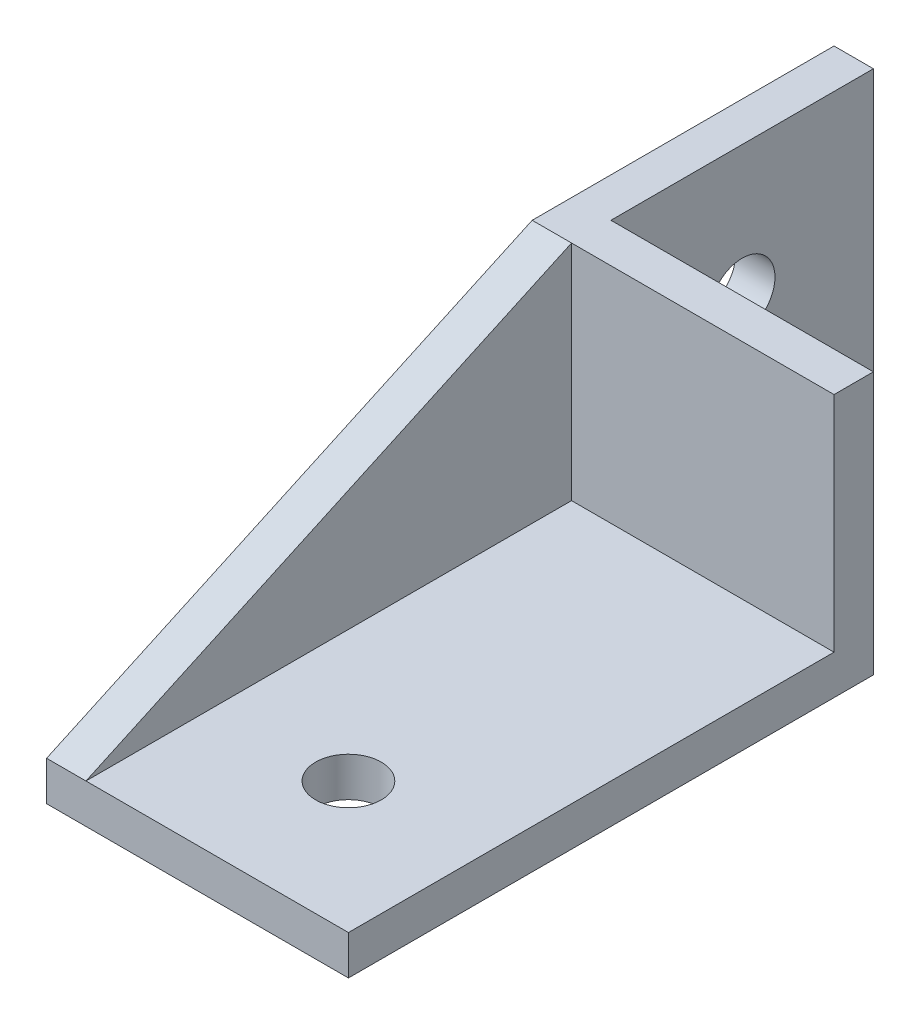
SolidWorks part; units mm, degrees
ref_plane "Front Plane" through (0, 0, 0) normal (0, 0, 1) x (1, 0, 0)
ref_plane "Top Plane" through (0, 0, 0) normal (0, 1, 0) x (1, 0, 0)
ref_plane "Right Plane" through (0, 0, 0) normal (1, 0, 0) x (0, 0, -1)
sketch "Sketch1" plane through (0, 0, 0) normal (0, 1, 0) x (1, 0, 0)
  line L1 (0, 0) -> (-3, 0)
  line L2 (0, 0) -> (0, 20)
  line L3 (0, 20) -> (-3, 20)
  line L4 (-3, 0) -> (-3, 20)
  line L5 (-3, 0) -> (20, 0)
  line L6 (-3, 0) -> (-3, -3)
  line L7 (-3, -3) -> (20, -3)
  line L8 (20, 0) -> (20, -3)
  dimension "D1" = 20
  dimension "D2" = 3
  dimension "D3" = 20
  dimension "D4" = 3
extrude "Boss-Extrude1" add sketch "Sketch1" along normal blind 20 contours L8 L5 L1 L6 L7 | L4 L1 L2 L3
sketch "Sketch3" plane through (0, 0, 0) normal (0, -1, 0) x (1, 0, 0)
  line L1 (20, 0) -> (0, 0)
  line L2 (20, 0) -> (20, 40)
  line L3 (20, 40) -> (0, 40)
  line L4 (0, 0) -> (0, 40)
  dimension "D1" = 20
  dimension "D2" = 40
extrude "Boss-Extrude2" add sketch "Sketch3" against normal blind 3
sketch "Sketch4" plane through (-3, 0, 0) normal (-1, 0, 0) x (0, 0, 1)
  line L0 (3, 20) -> (3, 0)
  line L1 (3, 0) -> (40, 0)
  line L2 (40, 0) -> (40, 3)
  line L3 (40, 3) -> (3, 20)
extrude "Boss-Extrude3" add sketch "Sketch4" against normal up to surface (3 mm away) up to face at (0, 1.5, 21.5)
sketch "Sketch5" plane through (0, 0, 0) normal (1, 0, 0) x (0, 0, -1)
  circle A0 centre (10, 10) radius 2.5
  dimension "D1" = 5
extrude "Cut-Extrude1" cut sketch "Sketch5" against normal blind 3
sketch "Sketch6" plane through (0, 3, 0) normal (0, 1, 0) x (1, 0, 0)
  line L0 (20, -40) -> (0, -40) construction
  circle A0 centre (10, -30) radius 2.5
  dimension "D1" = 10
  dimension "D2" = 5
extrude "Cut-Extrude2" cut sketch "Sketch6" against normal blind 3
